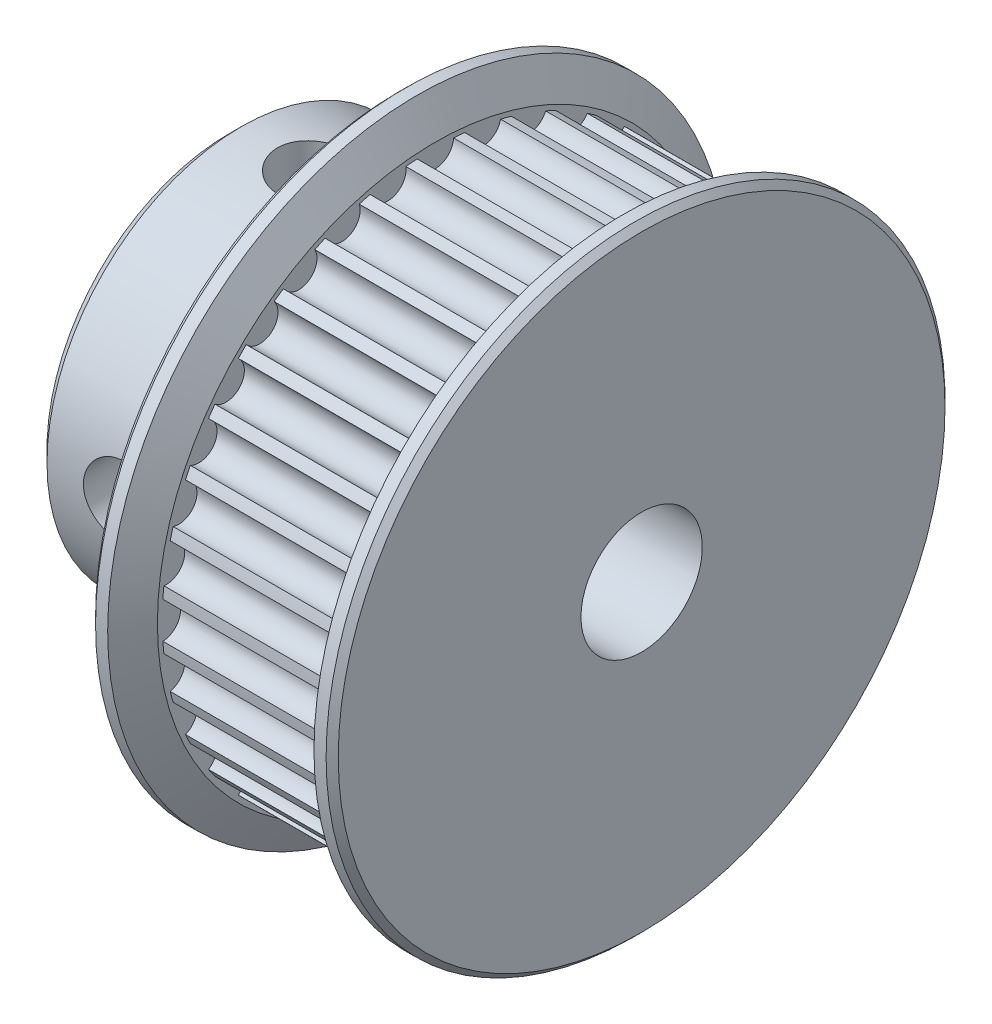
SolidWorks part; units mm, degrees
material "Lega 6061"
ref_plane "Piano frontale" through (0, 0, 0) normal (0, 0, 1) x (1, 0, 0)
ref_plane "Piano superiore" through (0, 0, 0) normal (0, 1, 0) x (1, 0, 0)
ref_plane "Piano destro" through (0, 0, 0) normal (1, 0, 0) x (0, 0, -1)
sketch "Schizzo4" plane through (0, 0, 0) normal (0, 0, 1) x (1, 0, 0)
  line L0 (0, 0) -> (25.6817, 0) construction
  line L1 (0, 2.5) -> (0, 8)
  line L2 (0, 8) -> (7, 8)
  line L3 (7, 8) -> (7, 12.75)
  line L4 (7, 12.75) -> (7.75, 12.75)
  line L5 (7.75, 12.75) -> (8.5, 11.451)
  line L6 (8.5, 11.451) -> (8.5, 11.25)
  line L7 (8.5, 11.25) -> (15.5, 11.25)
  line L8 (15.5, 11.25) -> (15.5, 11.451)
  line L9 (15.5, 11.451) -> (16.25, 12.75)
  line L10 (16.25, 12.75) -> (17, 12.75)
  line L11 (17, 12.75) -> (17, 2.5)
  line L12 (17, 2.5) -> (0, 2.5)
  line L13 (12, 11.25) -> (12, 0) construction
  point P4 (14, 10.1519)
  point P6 (10, 11.744)
  point P17 (14, 11.5435)
  point P18 (14, 11.744)
  point P19 (15.5, 11.6454)
  point P20 (16.2331, 12.75)
  point P21 (7.8845, 12.75)
  point P24 (15.976, 12.75)
  point P25 (8.7755, 12.75)
  point P26 (15.7832, 12.75)
  point P27 (14, 11.7583)
  dimension "D1" = 7
  dimension "D2" = 5
  dimension "D3" = 17
  dimension "D4" = 5
  dimension "D5" = 16
  dimension "D6" = 25.5
  dimension "D7" = 22.5
  dimension "D8" = 1.5
  dimension "D9" = 0.75
  dimension "D10" = 60
revolve "Rivoluzione1" add sketch "Schizzo4" angle 360 about L0
sketch "Schizzo5" plane through (8.5, 0, 0) normal (1, 0, 0) x (0, 0, -1)
  circle A0 centre (0, 11.25) radius 0.75
  circle A1 centre (0, 0) radius 11.25 construction
  circle A29 centre (1.9535, 11.0791) radius 0.75
  circle A30 centre (3.8477, 10.5715) radius 0.75
  circle A31 centre (5.625, 9.7428) radius 0.75
  circle A32 centre (7.2314, 8.618) radius 0.75
  circle A33 centre (8.618, 7.2314) radius 0.75
  circle A34 centre (9.7428, 5.625) radius 0.75
  circle A35 centre (10.5715, 3.8477) radius 0.75
  circle A36 centre (11.0791, 1.9535) radius 0.75
  circle A37 centre (11.25, 0) radius 0.75
  circle A38 centre (11.0791, -1.9535) radius 0.75
  circle A39 centre (10.5715, -3.8477) radius 0.75
  circle A40 centre (9.7428, -5.625) radius 0.75
  circle A41 centre (8.618, -7.2314) radius 0.75
  circle A42 centre (7.2314, -8.618) radius 0.75
  circle A43 centre (5.625, -9.7428) radius 0.75
  circle A44 centre (3.8477, -10.5715) radius 0.75
  circle A45 centre (1.9535, -11.0791) radius 0.75
  circle A46 centre (0, -11.25) radius 0.75
  circle A47 centre (-1.9535, -11.0791) radius 0.75
  circle A48 centre (-3.8477, -10.5715) radius 0.75
  circle A49 centre (-5.625, -9.7428) radius 0.75
  circle A50 centre (-7.2314, -8.618) radius 0.75
  circle A51 centre (-8.618, -7.2314) radius 0.75
  circle A52 centre (-9.7428, -5.625) radius 0.75
  circle A53 centre (-10.5715, -3.8477) radius 0.75
  circle A54 centre (-11.0791, -1.9535) radius 0.75
  circle A55 centre (-11.25, 0) radius 0.75
  circle A56 centre (-11.0791, 1.9535) radius 0.75
  circle A57 centre (-10.5715, 3.8477) radius 0.75
  circle A58 centre (-9.7428, 5.625) radius 0.75
  circle A59 centre (-8.618, 7.2314) radius 0.75
  circle A60 centre (-7.2314, 8.618) radius 0.75
  circle A61 centre (-5.625, 9.7428) radius 0.75
  circle A62 centre (-3.8477, 10.5715) radius 0.75
  circle A63 centre (-1.9535, 11.0791) radius 0.75
  point P78 (0, 0)
  dimension "D1" = 1.5
  dimension "D2" = 36
extrude "Taglio-Estrusione1" cut sketch "Schizzo5" against normal up to surface (7 mm away)
sketch "Schizzo6" plane through (0, 0, 0) normal (0, 0, 1) x (1, 0, 0)
  line L0 (0, 0) -> (23.7398, 0) construction
  line L1 (3.5, 8) -> (3.5, -8) construction
  line L2 (7, 8) -> (0, 8) construction
  line L3 (0, -8) -> (7, -8) construction
  circle A0 centre (3.5, 0) radius 1.5
  dimension "D1" = 3
extrude "Taglio-Estrusione2" cut sketch "Schizzo6" along normal up to surface (8 mm away) up to face at (0, 0, 8)
cosmetic thread "Filettatura cosmetica2" parameters "D2"=4
sketch "Schizzo7" plane through (0, 0, 0) normal (0, 1, 0) x (1, 0, 0)
  line L0 (3.5, 8) -> (3.5, -7.8581) construction
  line L1 (7, 8) -> (0, 8) construction
  circle A0 centre (3.5, 0) radius 1.5
  spline S0 degree 2 poles (2, -8) (3.5, -7.7188) (5, -8) knots 0 0 0 1 1 1 weights 0.0065 0.008 0.0095 construction
  dimension "D1" = 3
extrude "Taglio-Estrusione3" cut sketch "Schizzo7" along normal up to surface (7.8581 mm away)
cosmetic thread "Filettatura cosmetica1" parameters "D2"=4
chamfer "Smusso1" distance 0.5 angle 45 2 edges at (0, 0, 8) (0, 0, 2.5)
chamfer "Smusso2" distance 0.25 angle 45 2 edges at (17, 0, 12.75) (7, 0, 12.75)
